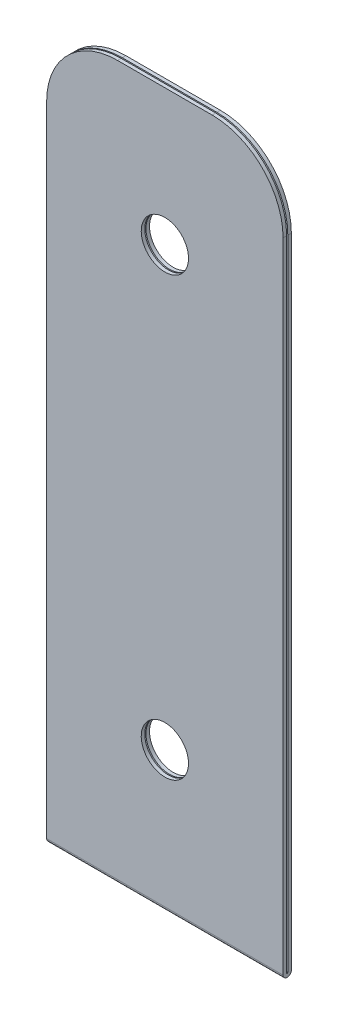
SolidWorks part; units mm, degrees
ref_plane "Front Plane" through (0, 0, 0) normal (0, 0, 1) x (1, 0, 0)
ref_plane "Top Plane" through (0, 0, 0) normal (0, 1, 0) x (1, 0, 0)
ref_plane "Right Plane" through (0, 0, 0) normal (1, 0, 0) x (0, 0, -1)
sketch "Sketch1" plane through (0, 0, 0) normal (1, 0, 0) x (0, 0, -1)
  line L0 (0, 30) -> (0, 0)
  line L1 (0, 30) -> (0.15, 30)
  line L2 (0.15, 30) -> (0.15, 0)
  line L3 (-0.05, 30) -> (-0.05, 0)
  line L4 (-0.2, 30) -> (-0.2, 0)
  line L5 (-0.05, 30) -> (-0.2, 30)
  arc A0 (0, 0) -> (-0.05, 0) centre (-0.025, 0) cw
  arc A1 (0.15, 0) -> (-0.2, 0) centre (-0.025, 0) cw
  dimension "D1" = 0.15
  dimension "D2" = 0.05
  dimension "D3" = 30
extrude "Boss-Extrude1" add sketch "Sketch1" along normal blind 10
fillet "Fillet1" radius 3 4 edges at (0, 30, 0.125) (10, 30, 0.125) (0, 30, -0.075) (10, 30, -0.075)
sketch "Sketch2" plane through (0, 0, 0.2) normal (0, 0, 1) x (1, 0, 0)
  line L0 (5, 24.25) -> (0, 24.25)
  line L1 (5, 24.25) -> (10, 24.25)
  line L2 (5, 24.25) -> (5, 30)
  line L3 (5, 5.75) -> (5, 0)
  line L4 (7, 30) -> (3, 30)
  line L5 (0, 27) -> (0, 0)
  line L6 (0, 0) -> (10, 0)
  line L7 (10, 0) -> (10, 27)
  line L8 (7, 30) -> (3, 30)
  line L9 (0, 27) -> (0, 0)
  line L10 (0, 0) -> (10, 0)
  line L11 (10, 0) -> (10, 27)
  circle A0 centre (5, 24.25) radius 1
  circle A1 centre (5, 5.75) radius 1
  arc A2 (3, 30) -> (0, 27) centre (3, 27) ccw
  arc A3 (10, 27) -> (7, 30) centre (7, 27) ccw
  arc A4 (3, 30) -> (0, 27) centre (3, 27) ccw
  arc A5 (10, 27) -> (7, 30) centre (7, 27) ccw
  dimension "D2" = 18.5
  dimension "D3" = 2
  dimension "D4" = 5.75
  dimension "D1" = 0
extrude "Cut-Extrude1" cut sketch "Sketch2" against normal through all both and the other way through all
